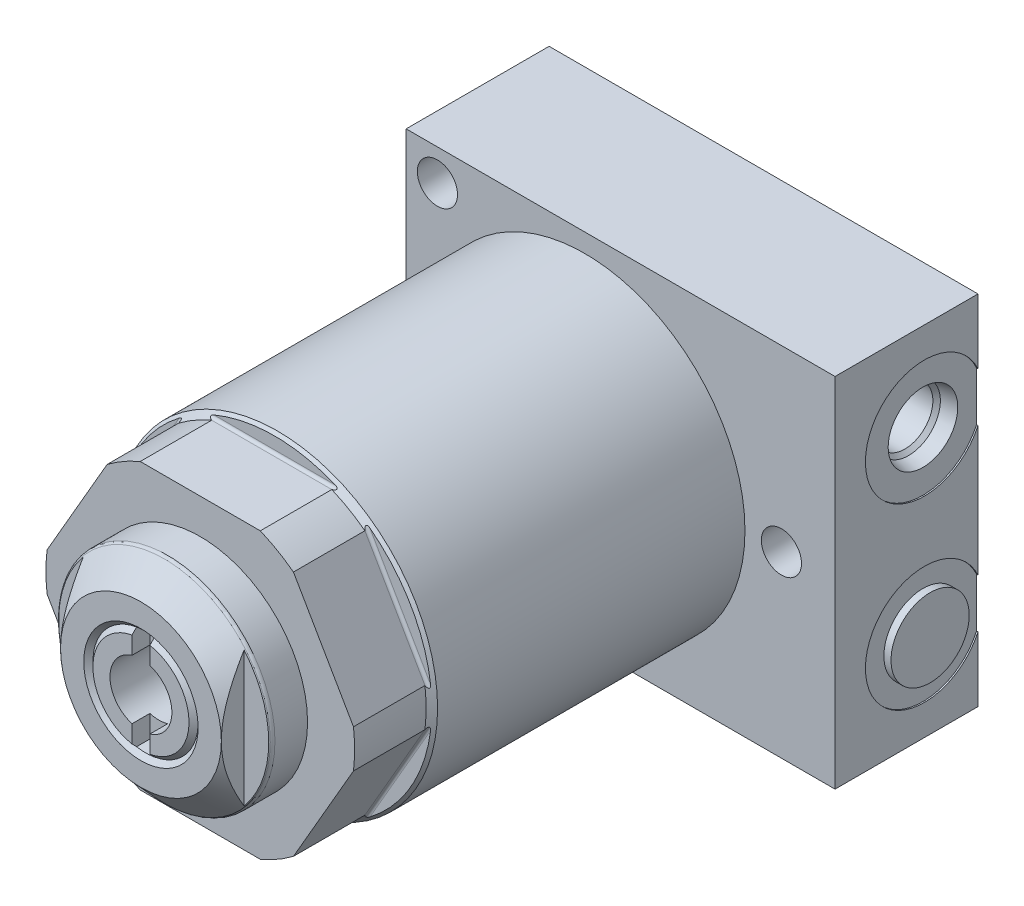
SolidWorks part; units mm, degrees
material "Alloy Steel"
ref_plane "Front Plane" through (0, 0, 0) normal (0, 0, 1) x (1, 0, 0)
ref_plane "Top Plane" through (0, 0, 0) normal (0, 1, 0) x (1, 0, 0)
ref_plane "Right Plane" through (0, 0, 0) normal (1, 0, 0) x (0, 0, -1)
ref_plane "Plane1" through (0, 0, 0) normal (0, 0, 1) x (1, 0, 0)
sketch "Sketch1" plane through (0, 0, 0) normal (0, 0, 1) x (1, 0, 0)
  circle A0 centre (0, 0) radius 28.448
  dimension "D1" = 56.896
extrude "Extrude1" add sketch "Sketch1" along normal blind 82.55
ref_plane "Plane2" through (0, 0, 0) normal (1, 0, 0) x (0, 0, 1)
sketch "Sketch2" plane through (0, 0, 0) normal (1, 0, 0) x (0, 0, 1)
  line L0 (69.342, 28.448) -> (69.342, 25.781)
  line L1 (69.85, 25.273) -> (82.55, 25.273)
  line L2 (68.6816, 0) -> (83.2104, 0) construction
  line L3 (82.55, -28.448) -> (82.55, 28.448) construction
  line L4 (69.342, 28.448) -> (82.55, 28.448)
  line L5 (82.55, 28.448) -> (82.55, 25.273)
  arc A0 (69.342, 25.781) -> (69.85, 25.273) centre (69.85, 25.781) ccw
  dimension "D2" = 0.508
  dimension "D1" = 50.546
  dimension "D3" = 13.208
extrude "Cut-Extrude1" cut sketch "Sketch2" against normal mid plane 68.2752
ref_plane "Plane12" through (0, 0, 0) normal (1, 0, 0) x (0, 0, -1)
sketch "Sketch10" plane through (0, 0, 0) normal (1, 0, 0) x (0, 0, -1)
  line L0 (-82.55, 27.432) -> (-69.85, 27.432)
  line L1 (-69.85, 27.432) -> (-68.834, 28.448)
  line L2 (-68.834, 28.448) -> (-82.55, 28.448)
  line L3 (-82.55, 28.448) -> (-82.55, 27.432)
  line L4 (-83.2358, 0) -> (-68.1482, 0) construction
  line L5 (0, 28.448) -> (-82.55, 28.448) construction
  line L6 (-82.55, 28.448) -> (-82.55, -25.273) construction
  dimension "D1" = 54.864
  dimension "D2" = 12.7
  dimension "D3" = 45
revolve "Cut-Revolve1" cut sketch "Sketch10" angle 360 about L4
ref_plane "Plane15" through (0, 0, 0) normal (1, 0, 0) x (0, 0, -1)
sketch "Sketch13" plane through (0, 0, 0) normal (1, 0, 0) x (0, 0, -1)
  line L0 (-82.55, 0) -> (-93.091, 0)
  line L1 (-93.091, 0) -> (-93.091, 19.0627)
  line L2 (-93.091, 19.0627) -> (-82.55, 19.0627)
  line L3 (-82.55, 19.0627) -> (-82.55, 0)
  line L4 (-93.618, 0) -> (-59.2792, 0) construction
  line L5 (-82.55, 27.432) -> (-82.55, -25.273) construction
  dimension "D1" = 38.1254
  dimension "D2" = 10.541
revolve "Revolve1" add sketch "Sketch13" angle 360 about L4
ref_plane "Plane16" through (-5.4991, 0, 93.091) normal (0, 1, 0) x (-1, 0, 0)
sketch "S2D0011" plane through (-5.4991, 0, 93.091) normal (0, 1, 0) x (-1, 0, 0)
  line L0 (0, 0) -> (0, -16.002)
  line L1 (0, -16.002) -> (-5.4991, -16.002)
  line L2 (0, 0) -> (-5.4991, 0)
  line L3 (-5.4991, 0) -> (-5.4991, -16.002)
  line L4 (-5.4991, -36.8381) -> (-5.4991, 0.8001) construction
  line L5 (13.5636, 0) -> (-24.5618, 0) construction
  dimension "D1" = 10.9982
  dimension "D2" = 16.002
revolve "Cut-Revolve4" cut sketch "S2D0011" angle 360 about L4
ref_plane "Plane17" through (0, 0, 0) normal (1, 0, 0) x (0, 0, -1)
sketch "Sketch15" plane through (0, 0, 0) normal (1, 0, 0) x (0, 0, -1)
  line L0 (-93.091, 14.2875) -> (-88.92, 18.8092)
  line L1 (-93.3285, 0) -> (-72.8226, 0) construction
  line L2 (-93.091, 19.0627) -> (-93.091, -19.0627) construction
  line L3 (-82.55, 19.0627) -> (-93.091, 19.0627) construction
  line L4 (-93.091, 19.0627) -> (-93.091, 14.2875)
  line L5 (-88.3412, 19.0627) -> (-93.091, 19.0627)
  arc A0 (-88.3412, 19.0627) -> (-88.92, 18.8092) centre (-88.3412, 18.2753) ccw
  dimension "D2" = 0.7874
  dimension "D1" = 28.575
  dimension "D3" = 4.7498
revolve "Cut-Revolve5" cut sketch "Sketch15" angle 360 about L1
ref_plane "Plane18" through (0, 0, 0) normal (0, 1, 0) x (-1, 0, 0)
sketch "Sketch16" plane through (0, 0, 0) normal (0, 1, 0) x (-1, 0, 0)
  line L0 (-44.45, -11.176) -> (31.75, -11.176)
  line L1 (31.75, -11.176) -> (31.75, 14.224)
  line L2 (31.75, 14.224) -> (-44.45, 14.224)
  line L3 (-44.45, 14.224) -> (-44.45, -11.176)
  line L4 (-28.448, 0) -> (28.448, 0) construction
  dimension "D1" = 11.176
  dimension "D2" = 76.2
  dimension "D3" = 31.75
  dimension "D4" = 25.4
extrude "Extrude2" add sketch "Sketch16" along normal blind 31.75 and the other way blind 31.75
sketch "Sketch17" plane through (44.45, 0, 0) normal (1, 0, 0) x (0, 0, -1)
  circle A0 centre (1.651, -15.875) radius 10.4775
extrude "Cut-Extrude9" cut sketch "Sketch17" against normal blind 0.254
sketch "Sketch18" plane through (44.45, 0, 0) normal (1, 0, 0) x (0, 0, -1)
  circle A0 centre (1.651, 15.875) radius 10.4775
extrude "Cut-Extrude10" cut sketch "Sketch18" against normal blind 0.254
ref_plane "Plane19" through (44.196, -15.875, -1.651) normal (0, 0, 1) x (0, -1, 0)
sketch "S2D0002" plane through (44.196, -15.875, -1.651) normal (0, 0, 1) x (0, -1, 0)
  line L0 (0, 0) -> (6.1849, 0)
  line L1 (6.1849, 0) -> (5.6423, -2.5527)
  line L2 (5.6423, -2.5527) -> (4.9784, -3.2166)
  line L3 (4.9784, -3.2166) -> (4.9784, -17.272)
  line L4 (4.9784, -17.272) -> (0, -17.272)
  line L5 (0, -17.272) -> (0, 0)
  line L6 (0, -18.1356) -> (0, 0.8636) construction
  dimension "D1" = 17.272
revolve "Cut-Revolve6" cut sketch "S2D0002" angle 360 about L6
ref_plane "Plane20" through (44.196, 15.875, -1.651) normal (0, 0, 1) x (0, -1, 0)
sketch "S2D0001" plane through (44.196, 15.875, -1.651) normal (0, 0, 1) x (0, -1, 0)
  line L0 (0, 0) -> (6.1849, 0)
  line L1 (6.1849, 0) -> (5.6423, -2.5527)
  line L2 (5.6423, -2.5527) -> (4.9784, -3.2166)
  line L3 (4.9784, -3.2166) -> (4.9784, -17.272)
  line L4 (4.9784, -17.272) -> (0, -17.272)
  line L5 (0, -17.272) -> (0, 0)
  line L6 (0, -18.1356) -> (0, 0.8636) construction
  dimension "D1" = 17.272
revolve "Cut-Revolve7" cut sketch "S2D0001" angle 360 about L6
sketch "Sketch21" plane through (44.196, 0, 0) normal (1, 0, 0) x (0, 0, -1)
  circle A0 centre (1.651, -15.875) radius 6.9469
extrude "Extrude3" add sketch "Sketch21" along normal blind 1.27
pattern_circular "CirPattern2" count 6 over 360 about axis through (0, 0, 0) along (0, 0, 1) of "Cut-Extrude1"
hole_wizard "Hole1" positions "Sketch23" profile "Sketch22" legacy end condition up to next
sketch "Sketch23" plane through (0, 0, 14.224) normal (0, 0, 1) x (1, 0, 0)
  line L0 (0, 0) -> (-36.1015, 0) construction
  point P0 (-26.1874, -26.1874)
  point P6 (34.925, 0)
  point P10 (-26.1874, 26.1874)
  dimension "D1" = 34.925
  dimension "D2" = 26.1874
  dimension "D3" = 26.1874
  dimension "D4" = 52.3748
sketch "Sketch22" plane through (-26.1874, -26.1874, 14.224) normal (1, 0, 0) x (0, -1, 0)
  line L0 (0, 0) -> (0, 25.4)
  line L1 (0, 25.4) -> (3.5687, 25.4)
  line L2 (3.5687, 25.4) -> (3.5687, 0)
  line L3 (3.5687, 0) -> (0, 0)
  line L4 (0, 110) -> (0, -10) construction
  dimension "Diameter" = 7.1374
  dimension "Depth" = 25.4
sketch "Sketch24" plane through (0, 0, 0) normal (1, 0, 0) x (0, 0, -1)
  line L0 (-93.091, 8.5344) -> (-92.2782, 9.3472)
  line L1 (-92.2782, 9.3472) -> (-93.091, 10.16)
  line L2 (-93.091, 10.16) -> (-93.091, 8.5344)
  line L3 (-93.1316, 0) -> (-86.5532, 0) construction
  line L4 (-93.091, 14.2875) -> (-93.091, -14.2875) construction
  dimension "D1" = 9.3472
  dimension "D2" = 1.6256
  dimension "D3" = 90
  dimension "D4" = 45
revolve "Cut-Revolve8" cut sketch "Sketch24" angle 360 about L3
sketch "Sketch25" plane through (0, 0, 93.091) normal (0, 0, 1) x (1, 0, 0)
  line L0 (-1.5875, 9.2114) -> (-1.5875, -9.2114)
  line L1 (1.5875, -9.2114) -> (1.5875, 9.2114)
  line L2 (0, 0) -> (0, -17.1227) construction
  arc A0 (-1.5875, -9.2114) -> (1.5875, -9.2114) centre (0, 0) ccw
  arc A1 (1.5875, 9.2114) -> (-1.5875, 9.2114) centre (0, 0) ccw
  circle A2 centre (0, 0) radius 9.3472 construction
  dimension "D1" = 3.175
extrude "Cut-Extrude11" cut sketch "Sketch25" against normal blind 3.175
sketch "Sketch26" plane through (0, 0, 93.091) normal (0, 0, 1) x (1, 0, 0)
  line L0 (0, 0) -> (0, -45.0928) construction
  line L1 (-14.2875, 12.6196) -> (-14.2875, -12.6196)
  line L2 (14.2875, 12.6196) -> (14.2875, -12.6196)
  circle A0 centre (0, 0) radius 19.0627 construction
  arc A1 (14.2875, -12.6196) -> (14.2875, 12.6196) centre (0, 0) ccw
  arc A2 (-14.2875, 12.6196) -> (-14.2875, -12.6196) centre (0, 0) ccw
  dimension "D1" = 28.575
extrude "Cut-Extrude12" cut sketch "Sketch26" against normal blind 4.0386
